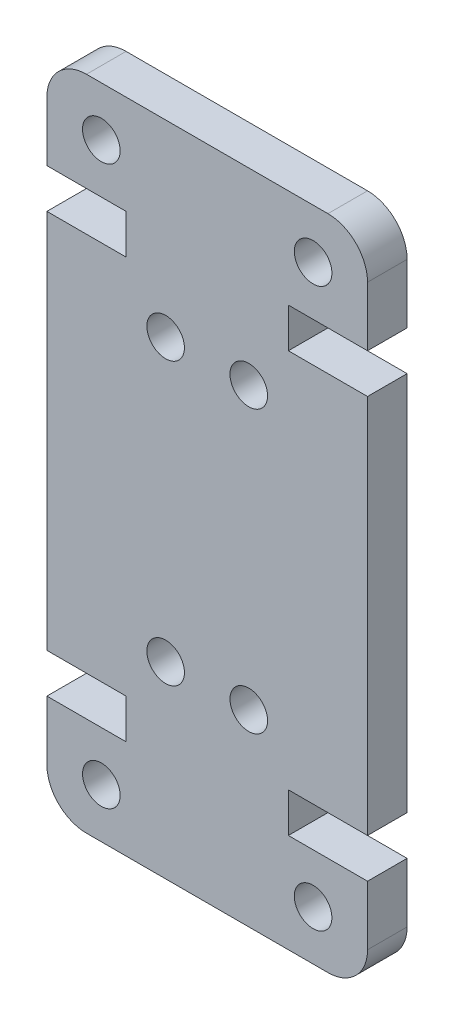
SolidWorks part; units mm, degrees
ref_plane "Front Plane" through (0, 0, 0) normal (0, 0, 1) x (1, 0, 0)
ref_plane "Top Plane" through (0, 0, 0) normal (0, 1, 0) x (1, 0, 0)
ref_plane "Right Plane" through (0, 0, 0) normal (1, 0, 0) x (0, 0, -1)
sketch "Sketch1" plane through (0, 0, 0) normal (0, 0, 1) x (1, 0, 0)
  line L0 (0, 26.21) -> (0, 7)
  line L1 (16.2, 2) -> (16.2, 5)
  line L2 (12.2, 5) -> (16.2, 5)
  line L3 (2, 0) -> (14.2, 0)
  line L4 (16.2, 7) -> (12.2, 7)
  line L5 (12.2, 7) -> (12.2, 5)
  line L6 (16.2, 26.21) -> (16.2, 7)
  line L7 (4, 7) -> (4, 5)
  line L8 (0, 31.21) -> (0, 28.21)
  line L9 (4, 28.21) -> (0, 28.21)
  line L10 (0, 7) -> (4, 7)
  line L11 (0, 26.21) -> (4, 26.21)
  line L12 (4, 5) -> (0, 5)
  line L13 (4, 26.21) -> (4, 28.21)
  line L14 (12.2, 26.21) -> (12.2, 28.21)
  line L15 (16.2, 26.21) -> (12.2, 26.21)
  line L16 (0, 2) -> (0, 5)
  line L17 (2, 33.21) -> (14.2, 33.21)
  line L18 (12.2, 28.21) -> (16.2, 28.21)
  line L19 (16.2, 31.21) -> (16.2, 28.21)
  line L20 (0, 16.605) -> (16.2, 16.605) construction
  line L21 (8.1, 33.21) -> (8.1, 0) construction
  circle A0 centre (13.45, 2.5) radius 0.95
  circle A1 centre (10.2, 9.5) radius 0.95
  arc A2 (16.2, 2) -> (14.2, 0) centre (14.2, 2) cw
  circle A3 centre (2.75, 30.71) radius 0.95
  circle A4 centre (6, 23.71) radius 0.95
  arc A5 (0, 2) -> (2, 0) centre (2, 2) ccw
  arc A6 (0, 31.21) -> (2, 33.21) centre (2, 31.21) cw
  circle A7 centre (6, 9.5) radius 0.95
  arc A8 (16.2, 31.21) -> (14.2, 33.21) centre (14.2, 31.21) ccw
  circle A9 centre (2.75, 2.5) radius 0.95
  circle A10 centre (10.2, 23.71) radius 0.95
  circle A11 centre (13.45, 30.71) radius 0.95
  point P15 (8.1, 16.605)
  dimension "D1" = 1.9
  dimension "D2" = 2
  dimension "D3" = 2.75
  dimension "D4" = 6
  dimension "D5" = 8.1
  dimension "D6" = 2.5
  dimension "D7" = 5
  dimension "D9" = 9.5
  dimension "D10" = 16.605
extrude "Boss-Extrude1" add sketch "Sketch1" along normal blind 4
sketch "Sketch2" plane through (0, 0, 0) normal (0, 0, 1) x (1, 0, 0)
  line L0 (0, 0) -> (16.2, 0)
  line L1 (16.2, 0) -> (16.2, 33.21)
  line L2 (16.2, 33.21) -> (0, 33.21)
  line L3 (0, 33.21) -> (0, 0)
extrude "Cut-Extrude2" cut sketch "Sketch2" along normal blind 2
equation "\"D5@Sketch1\"= \"fingerWidth@parametersSketch@prostheticParameters.SLDPRT\" / 2'PIP width"
equation "\"D10@Sketch1\"= ( \"HL@parametersSketch@prostheticParameters.SLDPRT\" * 0.266 - 12 - 4 ) / 2 'PIP length - Sil. sht PIP-Sil Sht MIP"
equation "\"D1@Sketch1\"= 1.5 + \"tol1@parametersSketch@prostheticParameters.SLDPRT\""
